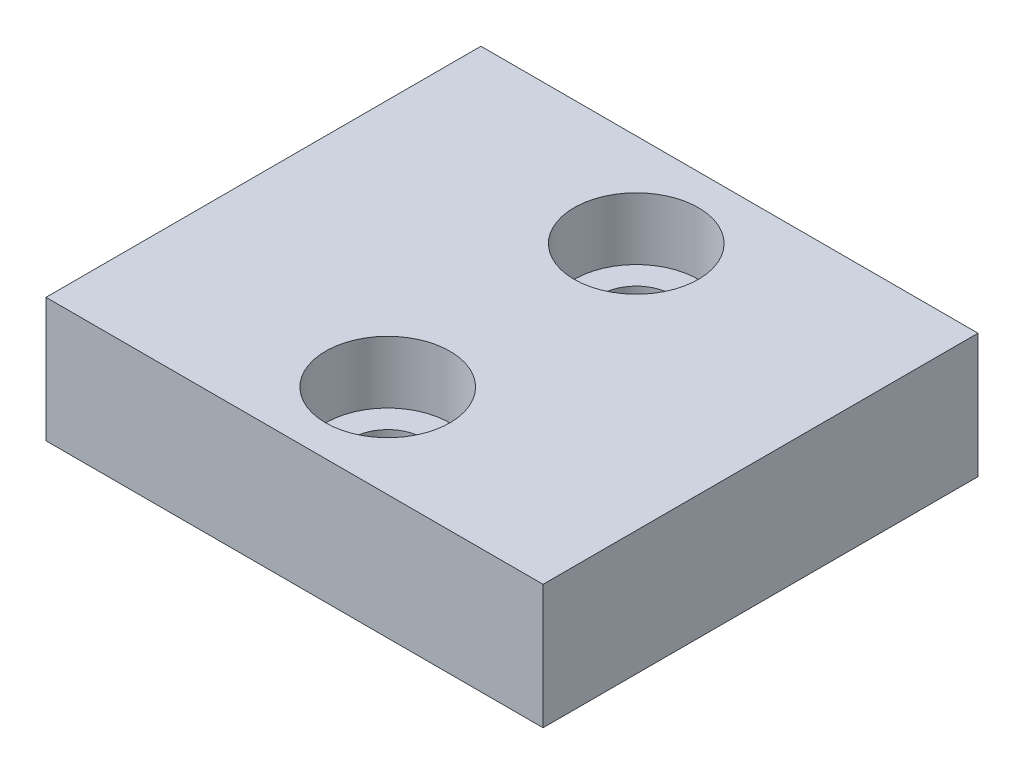
SolidWorks part; units mm, degrees
ref_plane "정면" through (0, 0, 0) normal (0, 0, 1) x (1, 0, 0)
ref_plane "윗면" through (0, 0, 0) normal (0, 1, 0) x (1, 0, 0)
ref_plane "우측면" through (0, 0, 0) normal (1, 0, 0) x (0, 0, -1)
sketch "스케치1" plane through (0, 0, 0) normal (0, 1, 0) x (1, 0, 0)
  line L1 (-8, 7) -> (8, 7)
  line L2 (-8, 7) -> (-8, -7)
  line L3 (-8, -7) -> (8, -7)
  line L4 (8, 7) -> (8, -7)
  circle A0 centre (0, 4) radius 1.15
  circle A1 centre (0, -4) radius 1.15
  point P8 (0, 7)
  point P10 (0, -7)
  point P11 (-8, 0)
  dimension "D5" = 2.3
  dimension "D1" = 4
  dimension "D2" = 4
  dimension "D3" = 14
  dimension "D4" = 16
extrude "보스-돌출1" add sketch "스케치1" along normal blind 4
sketch "스케치2" plane through (0, 4, 0) normal (0, 1, 0) x (1, 0, 0)
  circle A0 centre (0, 4) radius 2
  circle A1 centre (0, -4) radius 2
  dimension "D1" = 4
extrude "컷-돌출1" cut sketch "스케치2" against normal offset from surface (2 mm away) 2 up to face at (0, 0, 0)
